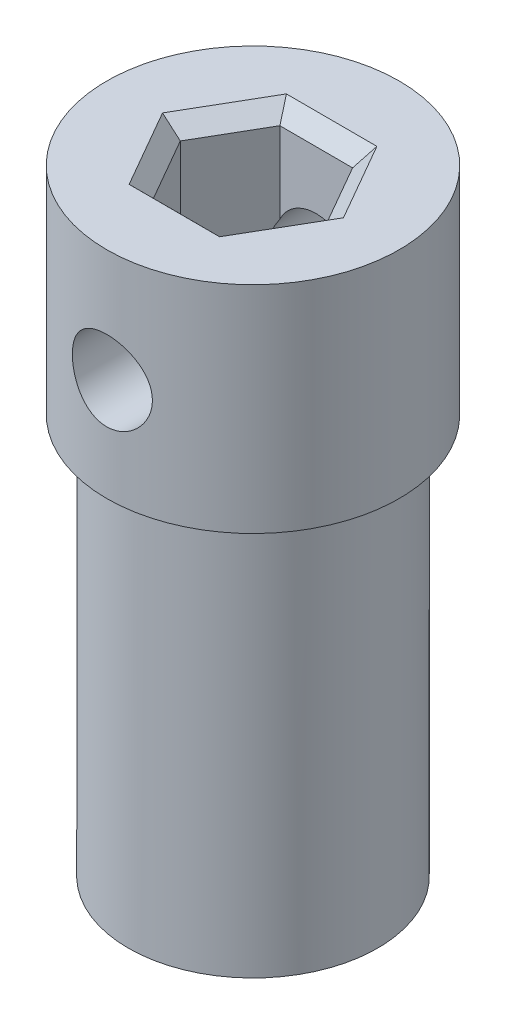
SolidWorks part; units mm, degrees
material "PLA"
ref_plane "Front Plane" through (0, 0, 0) normal (0, 0, 1) x (1, 0, 0)
ref_plane "Top Plane" through (0, 0, 0) normal (0, 1, 0) x (1, 0, 0)
ref_plane "Right Plane" through (0, 0, 0) normal (1, 0, 0) x (0, 0, -1)
sketch "Sketch1" plane through (0, 0, 0) normal (0, 1, 0) x (1, 0, 0)
  line L1 (1.1879, 2.0475) -> (-1.1793, 2.0525)
  line L2 (-1.1793, 2.0525) -> (-2.3671, 0.005)
  line L3 (-2.3671, 0.005) -> (-1.1879, -2.0475)
  line L4 (-1.1879, -2.0475) -> (1.1793, -2.0525)
  line L5 (1.1793, -2.0525) -> (2.3671, -0.005)
  line L6 (2.3671, -0.005) -> (1.1879, 2.0475)
  circle A0 centre (0, 0) radius 4.05
  circle A1 centre (0, 0) radius 2.05 construction
  dimension "D1" = 8.1
  dimension "D2" = 4.1
extrude "Boss-Extrude1" add sketch "Sketch1" along normal blind 20
sketch "Sketch2" plane through (0, 0, 0) normal (0, -1, 0) x (1, 0, 0)
  circle A1 centre (0, 0) radius 4.05
extrude "Boss-Extrude2" add sketch "Sketch2" against normal blind 5
ref_plane "Plane1" through (0, 13, 0) normal (0, -1, 0) x (-1, 0, 0)
sketch "Sketch3" plane through (0, 13, 0) normal (0, -1, 0) x (-1, 0, 0)
  circle A0 centre (0, 0) radius 4.05 construction
  circle A1 centre (0, 0) radius 4.05
  circle A2 centre (0, 0) radius 4.75
  dimension "D1" = 9.5
extrude "Boss-Extrude3" add sketch "Sketch3" against normal up to surface (7 mm away) up to face at (0, 20, 4.05)
chamfer "Chamfer1" distance 0.5 angle 45 6 edges at (-1.7775, 20, 1.0213) (-0.0043, 20, 2.05) (-1.7732, 20, -1.0287) (1.7732, 20, 1.0287) (1.7775, 20, -1.0213) (0.0043, 20, -2.05)
ref_plane "Plane2" through (0, 0, -4.75) normal (0, 0, -1) x (-1, 0, 0)
sketch "Sketch4" plane through (0, 0, -4.75) normal (0, 0, -1) x (-1, 0, 0)
  line L0 (0, 20.2923) -> (0, 12.346) construction
  line L1 (-4.75, 16.5) -> (4.75, 16.5) construction
  line L2 (-4.75, 20) -> (-4.75, 13) construction
  line L3 (4.75, 13) -> (4.75, 20) construction
  circle A0 centre (0, 16.3192) radius 1.3
extrude "Cut-Extrude1" cut sketch "Sketch4" against normal through all
